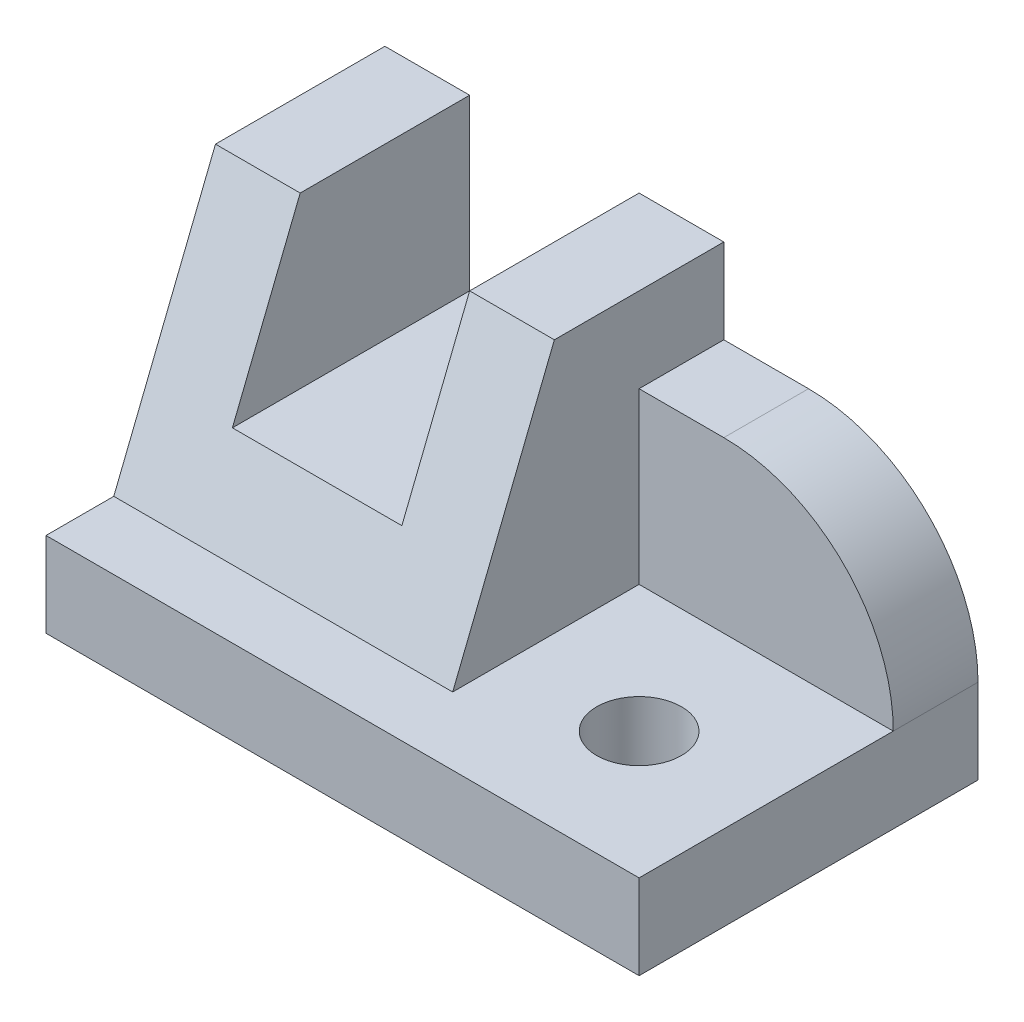
SolidWorks part; units mm, degrees
ref_plane "Front Plane" through (0, 0, 0) normal (0, 0, 1) x (1, 0, 0)
ref_plane "Top Plane" through (0, 0, 0) normal (0, 1, 0) x (1, 0, 0)
ref_plane "Right Plane" through (0, 0, 0) normal (1, 0, 0) x (0, 0, -1)
ref_plane "Plane1" through (0, 0, 0) normal (-1, 0, 0) x (0, -1, 0)
sketch "Sketch1" plane through (0, 0, 0) normal (-1, 0, 0) x (0, -1, 0)
  line L0 (-10, -8) -> (-40, -20)
  line L1 (-40, -20) -> (-10, -20)
  line L2 (-10, -20) -> (-10, -8)
  dimension "D1" = 30
  dimension "Width" = 12
extrude "Boss-Extrude1" add sketch "Sketch1" against normal blind 40
sketch "Sketch2" plane through (0, 0, -20) normal (0, 0, -1) x (-1, 0, 0)
  line L0 (-40, 40) -> (0, 40)
  line L1 (0, 40) -> (0, 10)
  line L2 (0, 10) -> (-40, 10)
  line L3 (-40, 10) -> (-40, 40)
extrude "Boss-Extrude2" add sketch "Sketch2" along normal blind 20
sketch "Sketch3" plane through (40, 0, 0) normal (1, 0, 0) x (0, 0, -1)
  line L0 (40, 10) -> (0, 10)
  line L1 (0, 10) -> (20, 40)
  line L2 (20, 40) -> (40, 40)
  line L3 (40, 40) -> (40, 10)
extrude "Boss-Extrude3" add sketch "Sketch3" along normal blind 30
sketch "Sketch4" plane through (70, 0, 0) normal (1, 0, 0) x (0, 0, -1)
  line L0 (20, 40) -> (0, 10)
  line L1 (0, 10) -> (30, 10)
  line L2 (30, 10) -> (30, 30)
  line L3 (30, 30) -> (40, 30)
  line L4 (40, 30) -> (40, 40)
  line L5 (40, 40) -> (20, 40)
extrude "Cut-Extrude1" cut sketch "Sketch4" against normal blind 30
sketch "Sketch5" plane through (0, 10, 0) normal (0, -1, 0) x (1, 0, 0)
  line L0 (70, 0) -> (70, -40)
  line L1 (70, -40) -> (0, -40)
  line L2 (0, -40) -> (0, 0)
  line L3 (0, 0) -> (70, 0)
extrude "Boss-Extrude4" add sketch "Sketch5" along normal blind 10
sketch "Sketch6" plane through (0, 0, -40) normal (0, 0, -1) x (-1, 0, 0)
  line L0 (-30, 40) -> (-30, 20)
  line L1 (-30, 20) -> (-10, 20)
  line L2 (-10, 20) -> (-10, 40)
  line L3 (-10, 40) -> (-30, 40)
extrude "Cut-Extrude2" cut sketch "Sketch6" against normal through all
hole_wizard "Ø10.0 (10) Diameter Hole1" positions "Sketch8" profile "Sketch7" hole size "Ø10.0" standard "ANSI Metric"
sketch "Sketch8" plane through (0, 0, 0) normal (0, -1, 0) x (-1, 0, 0)
  point P0 (-55, 15)
sketch "Sketch7" plane through (55, 0, -15) normal (1, 0, 0) x (0, 0, -1)
  line L0 (0, 0) -> (0, 40)
  line L1 (0, 40) -> (5, 40)
  line L2 (5, 40) -> (5, 0)
  line L5 (5, 0) -> (0, 0)
  line L11 (0, -6.35) -> (0, 107.95) construction
  dimension "Thru Hole Dia." = 10
  dimension "Thru Hole Depth" = 40
fillet "Fillet1" radius 20 1 edges at (70, 30, -35)
